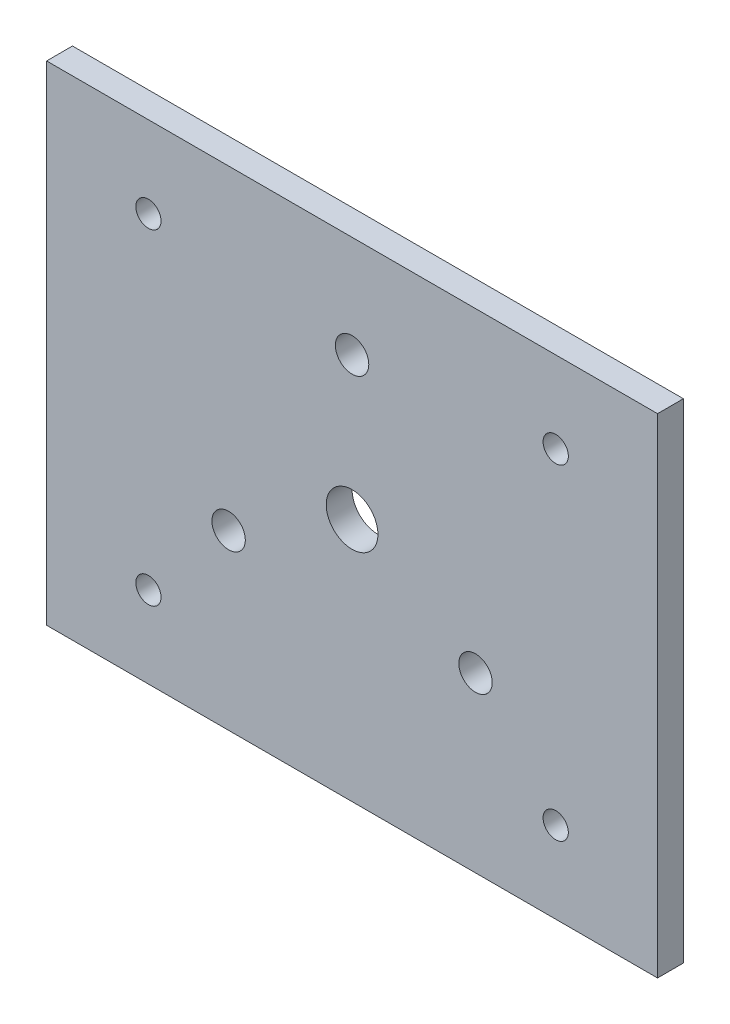
SolidWorks part; units mm, degrees
ref_plane "Alzado" through (0, 0, 0) normal (0, 0, 1) x (1, 0, 0)
ref_plane "Planta" through (0, 0, 0) normal (0, 1, 0) x (1, 0, 0)
ref_plane "Vista lateral" through (0, 0, 0) normal (1, 0, 0) x (0, 0, -1)
sketch "Croquis1" plane through (0, 0, 0) normal (0, 0, 1) x (1, 0, 0)
  line L0 (0, 35) -> (-30.3109, -17.5) construction
  line L1 (-75, 60) -> (75, 60)
  line L2 (-75, 60) -> (-75, -60)
  line L3 (-75, -60) -> (75, -60)
  line L4 (75, 60) -> (75, -60)
  line L5 (-75, 60) -> (75, -60) construction
  line L6 (-75, -60) -> (75, 60) construction
  line L7 (-30.3109, -17.5) -> (30.3109, -17.5) construction
  line L8 (30.3109, -17.5) -> (0, 35) construction
  line L9 (0, 35) -> (0, 0) construction
  line L10 (-50, 40) -> (-50, -40) construction
  line L12 (-30.3109, -17.5) -> (-30.3109, 35) construction
  line L13 (-30.3109, 35) -> (30.3109, 35) construction
  line L14 (30.3109, 35) -> (30.3109, -17.5) construction
  line L19 (-30.3109, 35) -> (30.3109, -17.5) construction
  line L25 (-50, -40) -> (50, -40) construction
  line L26 (50, -40) -> (50, 40) construction
  line L27 (50, 40) -> (-50, 40) construction
  circle A5 centre (0, 35) radius 4.1
  circle A6 centre (-50, -40) radius 3.1
  circle A7 centre (30.3109, -17.5) radius 4.1
  circle A8 centre (-30.3109, -17.5) radius 4.1
  circle A9 centre (50, -40) radius 3.1
  circle A10 centre (50, 40) radius 3.1
  circle A11 centre (-50, 40) radius 3.1
  circle A13 centre (0, 0) radius 6.35
  point P0 (0, 0)
  point P7 (0, 0)
  point P10 (0, 8.75)
  point P17 (0, 0)
  point P18 (0, 0)
  dimension "D3" = 35
  dimension "D4" = 8.2
  dimension "D9" = 6.2
  dimension "D10" = 6.2
  dimension "D11" = 6.2
  dimension "D12" = 6.2
  dimension "D13" = 40
  dimension "D15" = 12.7
  dimension "D1" = 120
  dimension "D2" = 150
  dimension "D6" = 52.5
  dimension "D7" = 100
  dimension "D8" = 80
  dimension "D14" = 50
  dimension "D5" = 3
extrude "Saliente-Extruir1" add sketch "Croquis1" along normal blind 6.35
